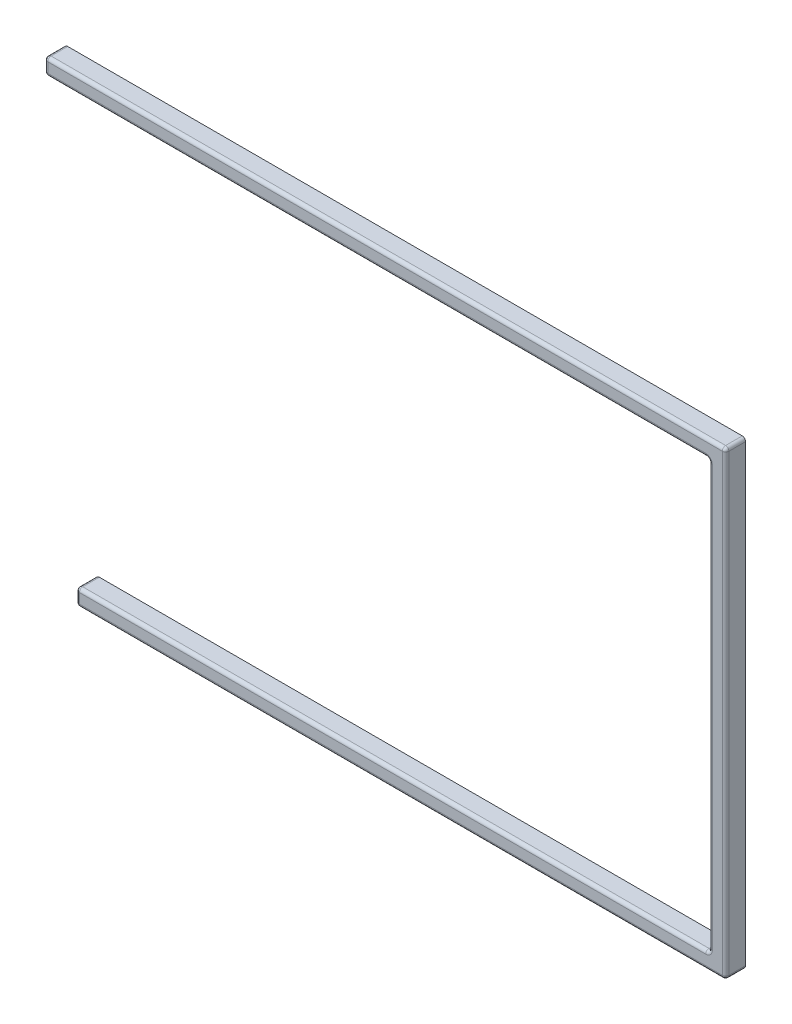
SolidWorks part; units mm, degrees
material "PA 类型 6"
ref_plane "前视基准面" through (0, 0, 0) normal (0, 0, 1) x (1, 0, 0)
ref_plane "上视基准面" through (0, 0, 0) normal (0, 1, 0) x (1, 0, 0)
ref_plane "右视基准面" through (0, 0, 0) normal (1, 0, 0) x (0, 0, -1)
other "Configuration Table"
sketch "Model" plane through (0, 0, 0) normal (0, 0, 1) x (1, 0, 0)
  line L0 (4.8569, 129.021) -> (204.883, 129.021)
  line L1 (204.883, 129.021) -> (204.883, 0.4341)
  line L2 (204.883, 0.4341) -> (14.3819, 0.4341)
  line L3 (21.3817, 112.498) -> (7.3822, 126.497) construction
  line L4 (145.495, 16.9595) -> (159.494, 16.9595)
  line L5 (159.494, 16.9595) -> (159.494, 2.96)
  line L6 (159.494, 2.96) -> (145.495, 2.96)
  line L7 (145.495, 2.96) -> (145.495, 16.9595)
  line L8 (164.545, 16.9595) -> (178.544, 16.9595)
  line L9 (178.544, 16.9595) -> (178.544, 2.96)
  line L10 (178.544, 2.96) -> (164.545, 2.96)
  line L11 (164.545, 2.96) -> (164.545, 16.9595)
  line L12 (183.595, 16.9595) -> (197.594, 16.9595)
  line L13 (197.594, 16.9595) -> (197.594, 2.96)
  line L14 (197.594, 2.96) -> (183.595, 2.96)
  line L15 (183.595, 2.96) -> (183.595, 16.9595)
  line L16 (33.5759, 21.722) -> (33.5759, 17.0215)
  line L17 (33.5759, 17.0215) -> (32.0504, 17.0215)
  line L18 (32.0504, 17.0215) -> (32.0504, 20.2517)
  line L19 (32.0504, 20.2517) -> (30.3251, 20.2517)
  line L20 (30.3251, 20.2517) -> (30.3251, 21.1722)
  line L21 (30.3251, 21.1722) -> (27.0261, 21.1722)
  line L22 (27.0261, 21.1722) -> (27.0261, 20.2517)
  line L23 (27.0261, 20.2517) -> (25.3008, 20.2517)
  line L24 (25.3008, 20.2517) -> (25.3008, 17.0215)
  line L25 (25.3008, 17.0215) -> (24.4753, 17.0215)
  line L26 (24.4753, 17.0215) -> (24.4753, 14.2227)
  line L27 (24.4753, 14.2227) -> (25.3008, 14.2227)
  line L28 (25.3008, 14.2227) -> (25.3008, 7.9527)
  line L29 (25.3008, 7.9527) -> (27.0261, 7.9527)
  line L30 (27.0261, 7.9527) -> (27.0261, 6.9729)
  line L31 (27.0261, 6.9729) -> (30.3251, 6.9729)
  line L32 (30.3251, 6.9729) -> (30.3251, 7.9527)
  line L33 (30.3251, 7.9527) -> (32.0504, 7.9527)
  line L34 (32.0504, 7.9527) -> (32.0504, 12.4216)
  line L35 (32.0504, 12.4216) -> (33.5759, 12.4216)
  line L36 (33.5759, 12.4216) -> (33.5759, 7.7225)
  line L37 (33.5759, 7.7225) -> (47.5753, 7.7225)
  line L38 (47.5753, 7.7225) -> (47.5753, 12.4216)
  line L39 (47.5753, 12.4216) -> (49.101, 12.4216)
  line L40 (49.101, 12.4216) -> (49.101, 7.9527)
  line L41 (49.101, 7.9527) -> (50.8247, 7.9527)
  line L42 (50.8247, 7.9527) -> (50.8247, 6.9729)
  line L43 (50.8247, 6.9729) -> (54.1253, 6.9729)
  line L44 (54.1253, 6.9729) -> (54.1253, 7.9527)
  line L45 (54.1253, 7.9527) -> (55.8504, 7.9527)
  line L46 (55.8504, 7.9527) -> (55.8504, 14.2227)
  line L47 (55.8504, 14.2227) -> (56.6759, 14.2227)
  line L48 (56.6759, 14.2227) -> (56.6759, 17.0215)
  line L49 (56.6759, 17.0215) -> (55.8504, 17.0215)
  line L50 (55.8504, 17.0215) -> (55.8504, 20.2517)
  line L51 (55.8504, 20.2517) -> (54.1253, 20.2517)
  line L52 (54.1253, 20.2517) -> (54.1253, 21.1722)
  line L53 (54.1253, 21.1722) -> (50.8247, 21.1722)
  line L54 (50.8247, 21.1722) -> (50.8247, 20.2517)
  line L55 (50.8247, 20.2517) -> (49.101, 20.2517)
  line L56 (49.101, 20.2517) -> (49.101, 17.0215)
  line L57 (49.101, 17.0215) -> (47.5753, 17.0215)
  line L58 (47.5753, 17.0215) -> (47.5753, 21.722)
  line L59 (47.5753, 21.722) -> (33.5759, 21.722)
  line L60 (71.676, 21.722) -> (85.6753, 21.722)
  line L61 (85.6753, 21.722) -> (85.6753, 7.7225)
  line L62 (85.6753, 7.7225) -> (71.676, 7.7225)
  line L63 (71.676, 7.7225) -> (71.676, 21.722)
  line L64 (95.4871, 21.722) -> (109.488, 21.722)
  line L65 (109.488, 21.722) -> (109.488, 7.7225)
  line L66 (109.488, 7.7225) -> (95.4871, 7.7225)
  line L67 (95.4871, 7.7225) -> (95.4871, 21.722)
  line L68 (119.301, 21.722) -> (133.3, 21.722)
  line L69 (133.3, 21.722) -> (133.3, 7.7225)
  line L70 (133.3, 7.7225) -> (119.301, 7.7225)
  line L71 (119.301, 7.7225) -> (119.301, 21.722)
  line L72 (164.545, 36.0094) -> (178.544, 36.0094)
  line L73 (178.544, 36.0094) -> (178.544, 22.01)
  line L74 (178.544, 22.01) -> (164.545, 22.01)
  line L75 (164.545, 22.01) -> (164.545, 36.0094)
  line L76 (26.4322, 40.7719) -> (40.4315, 40.7719)
  line L77 (40.4315, 40.7719) -> (40.4315, 26.7725)
  line L78 (40.4315, 26.7725) -> (26.4322, 26.7725)
  line L79 (26.4322, 26.7725) -> (26.4322, 40.7719)
  line L80 (45.4822, 40.7719) -> (59.4815, 40.7719)
  line L81 (59.4815, 40.7719) -> (59.4815, 26.7725)
  line L82 (59.4815, 26.7725) -> (45.4822, 26.7725)
  line L83 (45.4822, 26.7725) -> (45.4822, 40.7719)
  line L84 (64.5322, 40.7719) -> (78.5315, 40.7719)
  line L85 (78.5315, 40.7719) -> (78.5315, 26.7725)
  line L86 (78.5315, 26.7725) -> (64.5322, 26.7725)
  line L87 (64.5322, 26.7725) -> (64.5322, 40.7719)
  line L88 (83.5822, 40.7719) -> (97.5815, 40.7719)
  line L89 (97.5815, 40.7719) -> (97.5815, 26.7725)
  line L90 (97.5815, 26.7725) -> (83.5822, 26.7725)
  line L91 (83.5822, 26.7725) -> (83.5822, 40.7719)
  line L92 (102.632, 40.7719) -> (116.632, 40.7719)
  line L93 (116.632, 40.7719) -> (116.632, 26.7725)
  line L94 (116.632, 26.7725) -> (102.632, 26.7725)
  line L95 (102.632, 26.7725) -> (102.632, 40.7719)
  line L96 (128.826, 40.7719) -> (142.825, 40.7719)
  line L97 (142.825, 40.7719) -> (142.825, 26.7725)
  line L98 (142.825, 26.7725) -> (128.826, 26.7725)
  line L99 (128.826, 26.7725) -> (128.826, 40.7719)
  line L100 (188.357, 40.7719) -> (202.357, 40.7719)
  line L101 (202.357, 40.7719) -> (202.357, 26.7725)
  line L102 (202.357, 26.7725) -> (188.357, 26.7725)
  line L103 (188.357, 26.7725) -> (188.357, 40.7719)
  line L104 (143.112, 59.8219) -> (143.112, 55.1215)
  line L105 (143.112, 55.1215) -> (141.588, 55.1215)
  line L106 (141.588, 55.1215) -> (141.588, 58.3516)
  line L107 (141.588, 58.3516) -> (139.863, 58.3516)
  line L108 (139.863, 58.3516) -> (139.863, 59.2723)
  line L109 (139.863, 59.2723) -> (136.562, 59.2723)
  line L110 (136.562, 59.2723) -> (136.562, 58.3516)
  line L111 (136.562, 58.3516) -> (134.837, 58.3516)
  line L112 (134.837, 58.3516) -> (134.837, 55.1215)
  line L113 (134.837, 55.1215) -> (134.013, 55.1215)
  line L114 (134.013, 55.1215) -> (134.013, 52.3226)
  line L115 (134.013, 52.3226) -> (134.837, 52.3226)
  line L116 (134.837, 52.3226) -> (134.837, 46.0527)
  line L117 (134.837, 46.0527) -> (136.562, 46.0527)
  line L118 (136.562, 46.0527) -> (136.562, 45.0716)
  line L119 (136.562, 45.0716) -> (139.863, 45.0716)
  line L120 (139.863, 45.0716) -> (139.863, 46.0527)
  line L121 (139.863, 46.0527) -> (141.588, 46.0527)
  line L122 (141.588, 46.0527) -> (141.588, 50.5217)
  line L123 (141.588, 50.5217) -> (143.112, 50.5217)
  line L124 (143.112, 50.5217) -> (143.112, 45.8227)
  line L125 (143.112, 45.8227) -> (157.113, 45.8227)
  line L126 (157.113, 45.8227) -> (157.113, 50.5217)
  line L127 (157.113, 50.5217) -> (158.637, 50.5217)
  line L128 (158.637, 50.5217) -> (158.637, 46.0527)
  line L129 (158.637, 46.0527) -> (160.362, 46.0527)
  line L130 (160.362, 46.0527) -> (160.362, 45.0716)
  line L131 (160.362, 45.0716) -> (163.663, 45.0716)
  line L132 (163.663, 45.0716) -> (163.663, 46.0527)
  line L133 (163.663, 46.0527) -> (165.388, 46.0527)
  line L134 (165.388, 46.0527) -> (165.388, 52.3226)
  line L135 (165.388, 52.3226) -> (166.212, 52.3226)
  line L136 (166.212, 52.3226) -> (166.212, 55.1215)
  line L137 (166.212, 55.1215) -> (165.388, 55.1215)
  line L138 (165.388, 55.1215) -> (165.388, 58.3516)
  line L139 (165.388, 58.3516) -> (163.663, 58.3516)
  line L140 (163.663, 58.3516) -> (163.663, 59.2723)
  line L141 (163.663, 59.2723) -> (160.362, 59.2723)
  line L142 (160.362, 59.2723) -> (160.362, 58.3516)
  line L143 (160.362, 58.3516) -> (158.637, 58.3516)
  line L144 (158.637, 58.3516) -> (158.637, 55.1215)
  line L145 (158.637, 55.1215) -> (157.113, 55.1215)
  line L146 (157.113, 55.1215) -> (157.113, 59.8219)
  line L147 (157.113, 59.8219) -> (143.112, 59.8219)
  line L148 (16.9072, 59.8219) -> (30.9066, 59.8219)
  line L149 (30.9066, 59.8219) -> (30.9066, 45.8227)
  line L150 (30.9066, 45.8227) -> (16.9072, 45.8227)
  line L151 (16.9072, 45.8227) -> (16.9072, 59.8219)
  line L152 (35.9572, 59.8219) -> (49.9565, 59.8219)
  line L153 (49.9565, 59.8219) -> (49.9565, 45.8227)
  line L154 (49.9565, 45.8227) -> (35.9572, 45.8227)
  line L155 (35.9572, 45.8227) -> (35.9572, 59.8219)
  line L156 (55.0072, 59.8219) -> (69.0065, 59.8219)
  line L157 (69.0065, 59.8219) -> (69.0065, 45.8227)
  line L158 (69.0065, 45.8227) -> (55.0072, 45.8227)
  line L159 (55.0072, 45.8227) -> (55.0072, 59.8219)
  line L160 (74.0572, 59.8219) -> (88.0565, 59.8219)
  line L161 (88.0565, 59.8219) -> (88.0565, 45.8227)
  line L162 (88.0565, 45.8227) -> (74.0572, 45.8227)
  line L163 (74.0572, 45.8227) -> (74.0572, 59.8219)
  line L164 (93.1072, 59.8219) -> (107.107, 59.8219)
  line L165 (107.107, 59.8219) -> (107.107, 45.8227)
  line L166 (107.107, 45.8227) -> (93.1072, 45.8227)
  line L167 (93.1072, 45.8227) -> (93.1072, 59.8219)
  line L168 (112.157, 59.8219) -> (126.157, 59.8219)
  line L169 (126.157, 59.8219) -> (126.157, 45.8227)
  line L170 (126.157, 45.8227) -> (112.157, 45.8227)
  line L171 (112.157, 45.8227) -> (112.157, 59.8219)
  line L172 (188.357, 59.8219) -> (202.357, 59.8219)
  line L173 (202.357, 59.8219) -> (202.357, 45.8227)
  line L174 (202.357, 45.8227) -> (188.357, 45.8227)
  line L175 (188.357, 45.8227) -> (188.357, 59.8219)
  line L176 (12.1447, 78.8719) -> (26.1441, 78.8719)
  line L177 (26.1441, 78.8719) -> (26.1441, 64.8727)
  line L178 (26.1441, 64.8727) -> (12.1447, 64.8727)
  line L179 (12.1447, 64.8727) -> (12.1447, 78.8719)
  line L180 (31.1947, 78.8719) -> (45.194, 78.8719)
  line L181 (45.194, 78.8719) -> (45.194, 64.8727)
  line L182 (45.194, 64.8727) -> (31.1947, 64.8727)
  line L183 (31.1947, 64.8727) -> (31.1947, 78.8719)
  line L184 (50.2447, 78.8719) -> (64.244, 78.8719)
  line L185 (64.244, 78.8719) -> (64.244, 64.8727)
  line L186 (64.244, 64.8727) -> (50.2447, 64.8727)
  line L187 (50.2447, 64.8727) -> (50.2447, 78.8719)
  line L188 (69.2947, 78.8719) -> (83.294, 78.8719)
  line L189 (83.294, 78.8719) -> (83.294, 64.8727)
  line L190 (83.294, 64.8727) -> (69.2947, 64.8727)
  line L191 (69.2947, 64.8727) -> (69.2947, 78.8719)
  line L192 (88.3447, 78.8719) -> (102.344, 78.8719)
  line L193 (102.344, 78.8719) -> (102.344, 64.8727)
  line L194 (102.344, 64.8727) -> (88.3447, 64.8727)
  line L195 (88.3447, 64.8727) -> (88.3447, 78.8719)
  line L196 (107.395, 78.8719) -> (121.394, 78.8719)
  line L197 (121.394, 78.8719) -> (121.394, 64.8727)
  line L198 (121.394, 64.8727) -> (107.395, 64.8727)
  line L199 (107.395, 64.8727) -> (107.395, 78.8719)
  line L200 (126.445, 78.8719) -> (140.444, 78.8719)
  line L201 (140.444, 78.8719) -> (140.444, 64.8727)
  line L202 (140.444, 64.8727) -> (126.445, 64.8727)
  line L203 (126.445, 64.8727) -> (126.445, 78.8719)
  line L204 (150.257, 78.8719) -> (164.257, 78.8719)
  line L205 (164.257, 78.8719) -> (164.257, 64.8727)
  line L206 (164.257, 64.8727) -> (150.257, 64.8727)
  line L207 (150.257, 64.8727) -> (150.257, 78.8719)
  line L208 (188.357, 78.8719) -> (202.357, 78.8719)
  line L209 (202.357, 78.8719) -> (202.357, 64.8727)
  line L210 (202.357, 64.8727) -> (188.357, 64.8727)
  line L211 (188.357, 64.8727) -> (188.357, 78.8719)
  line L212 (145.493, 97.9219) -> (145.493, 93.2215)
  line L213 (145.493, 93.2215) -> (143.969, 93.2215)
  line L214 (143.969, 93.2215) -> (143.969, 96.4516)
  line L215 (143.969, 96.4516) -> (142.244, 96.4516)
  line L216 (142.244, 96.4516) -> (142.244, 97.3723)
  line L217 (142.244, 97.3723) -> (138.943, 97.3723)
  line L218 (138.943, 97.3723) -> (138.943, 96.4516)
  line L219 (138.943, 96.4516) -> (137.218, 96.4516)
  line L220 (137.218, 96.4516) -> (137.218, 93.2215)
  line L221 (137.218, 93.2215) -> (136.394, 93.2215)
  line L222 (136.394, 93.2215) -> (136.394, 90.4226)
  line L223 (136.394, 90.4226) -> (137.218, 90.4226)
  line L224 (137.218, 90.4226) -> (137.218, 84.1527)
  line L225 (137.218, 84.1527) -> (138.943, 84.1527)
  line L226 (138.943, 84.1527) -> (138.943, 83.1716)
  line L227 (138.943, 83.1716) -> (142.244, 83.1716)
  line L228 (142.244, 83.1716) -> (142.244, 84.1527)
  line L229 (142.244, 84.1527) -> (143.969, 84.1527)
  line L230 (143.969, 84.1527) -> (143.969, 88.6217)
  line L231 (143.969, 88.6217) -> (145.493, 88.6217)
  line L232 (145.493, 88.6217) -> (145.493, 83.9227)
  line L233 (145.493, 83.9227) -> (159.494, 83.9227)
  line L234 (159.494, 83.9227) -> (159.494, 88.6217)
  line L235 (159.494, 88.6217) -> (161.018, 88.6217)
  line L236 (161.018, 88.6217) -> (161.018, 84.1527)
  line L237 (161.018, 84.1527) -> (162.743, 84.1527)
  line L238 (162.743, 84.1527) -> (162.743, 83.1716)
  line L239 (162.743, 83.1716) -> (166.044, 83.1716)
  line L240 (166.044, 83.1716) -> (166.044, 84.1527)
  line L241 (166.044, 84.1527) -> (167.768, 84.1527)
  line L242 (167.768, 84.1527) -> (167.768, 90.4226)
  line L243 (167.768, 90.4226) -> (168.593, 90.4226)
  line L244 (168.593, 90.4226) -> (168.593, 93.2215)
  line L245 (168.593, 93.2215) -> (167.768, 93.2215)
  line L246 (167.768, 93.2215) -> (167.768, 96.4516)
  line L247 (167.768, 96.4516) -> (166.044, 96.4516)
  line L248 (166.044, 96.4516) -> (166.044, 97.3723)
  line L249 (166.044, 97.3723) -> (162.743, 97.3723)
  line L250 (162.743, 97.3723) -> (162.743, 96.4516)
  line L251 (162.743, 96.4516) -> (161.018, 96.4516)
  line L252 (161.018, 96.4516) -> (161.018, 93.2215)
  line L253 (161.018, 93.2215) -> (159.494, 93.2215)
  line L254 (159.494, 93.2215) -> (159.494, 97.9219)
  line L255 (159.494, 97.9219) -> (145.493, 97.9219)
  line L256 (2.6197, 97.9219) -> (16.6192, 97.9219)
  line L257 (16.6192, 97.9219) -> (16.6192, 83.9227)
  line L258 (16.6192, 83.9227) -> (2.6197, 83.9227)
  line L259 (2.6197, 83.9227) -> (2.6197, 97.9219)
  line L260 (21.6697, 97.9219) -> (35.669, 97.9219)
  line L261 (35.669, 97.9219) -> (35.669, 83.9227)
  line L262 (35.669, 83.9227) -> (21.6697, 83.9227)
  line L263 (21.6697, 83.9227) -> (21.6697, 97.9219)
  line L264 (40.7197, 97.9219) -> (54.719, 97.9219)
  line L265 (54.719, 97.9219) -> (54.719, 83.9227)
  line L266 (54.719, 83.9227) -> (40.7197, 83.9227)
  line L267 (40.7197, 83.9227) -> (40.7197, 97.9219)
  line L268 (59.7697, 97.9219) -> (73.769, 97.9219)
  line L269 (73.769, 97.9219) -> (73.769, 83.9227)
  line L270 (73.769, 83.9227) -> (59.7697, 83.9227)
  line L271 (59.7697, 83.9227) -> (59.7697, 97.9219)
  line L272 (78.8197, 97.9219) -> (92.819, 97.9219)
  line L273 (92.819, 97.9219) -> (92.819, 83.9227)
  line L274 (92.819, 83.9227) -> (78.8197, 83.9227)
  line L275 (78.8197, 83.9227) -> (78.8197, 97.9219)
  line L276 (97.8683, 97.9219) -> (111.869, 97.9219)
  line L277 (111.869, 97.9219) -> (111.869, 83.9227)
  line L278 (111.869, 83.9227) -> (97.8683, 83.9227)
  line L279 (97.8683, 83.9227) -> (97.8683, 97.9219)
  line L280 (116.918, 97.9219) -> (130.919, 97.9219)
  line L281 (130.919, 97.9219) -> (130.919, 83.9227)
  line L282 (130.919, 83.9227) -> (116.918, 83.9227)
  line L283 (116.918, 83.9227) -> (116.918, 97.9219)
  line L284 (188.357, 97.9219) -> (202.357, 97.9219)
  line L285 (202.357, 97.9219) -> (202.357, 83.9227)
  line L286 (202.357, 83.9227) -> (188.357, 83.9227)
  line L287 (188.357, 83.9227) -> (188.357, 97.9219)
  line L288 (7.3822, 126.497) -> (21.3817, 126.497)
  line L289 (21.3817, 126.497) -> (21.3817, 112.498)
  line L290 (21.3817, 112.498) -> (7.3822, 112.498)
  line L291 (7.3822, 112.498) -> (7.3822, 126.497)
  line L292 (26.4322, 126.497) -> (40.4315, 126.497)
  line L293 (40.4315, 126.497) -> (40.4315, 112.498)
  line L294 (40.4315, 112.498) -> (26.4322, 112.498)
  line L295 (26.4322, 112.498) -> (26.4322, 126.497)
  line L296 (45.4822, 126.497) -> (59.4815, 126.497)
  line L297 (59.4815, 126.497) -> (59.4815, 112.498)
  line L298 (59.4815, 112.498) -> (45.4822, 112.498)
  line L299 (45.4822, 112.498) -> (45.4822, 126.497)
  line L300 (64.5322, 126.497) -> (78.5315, 126.497)
  line L301 (78.5315, 126.497) -> (78.5315, 112.498)
  line L302 (78.5315, 112.498) -> (64.5322, 112.498)
  line L303 (64.5322, 112.498) -> (64.5322, 126.497)
  line L304 (83.5822, 126.497) -> (97.5815, 126.497)
  line L305 (97.5815, 126.497) -> (97.5815, 112.498)
  line L306 (97.5815, 112.498) -> (83.5822, 112.498)
  line L307 (83.5822, 112.498) -> (83.5822, 126.497)
  line L308 (102.632, 126.497) -> (116.632, 126.497)
  line L309 (116.632, 126.497) -> (116.632, 112.498)
  line L310 (116.632, 112.498) -> (102.632, 112.498)
  line L311 (102.632, 112.498) -> (102.632, 126.497)
  line L312 (121.682, 126.497) -> (135.682, 126.497)
  line L313 (135.682, 126.497) -> (135.682, 112.498)
  line L314 (135.682, 112.498) -> (121.682, 112.498)
  line L315 (121.682, 112.498) -> (121.682, 126.497)
  line L316 (145.495, 126.497) -> (159.494, 126.497)
  line L317 (159.494, 126.497) -> (159.494, 112.498)
  line L318 (159.494, 112.498) -> (145.495, 112.498)
  line L319 (145.495, 112.498) -> (145.495, 126.497)
  line L320 (164.545, 126.497) -> (178.544, 126.497)
  line L321 (178.544, 126.497) -> (178.544, 112.498)
  line L322 (178.544, 112.498) -> (164.545, 112.498)
  line L323 (164.545, 112.498) -> (164.545, 126.497)
  line L324 (185.976, 126.497) -> (199.975, 126.497)
  line L325 (199.975, 126.497) -> (199.975, 112.498)
  line L326 (199.975, 112.498) -> (185.976, 112.498)
  line L327 (185.976, 112.498) -> (185.976, 126.497)
  line L328 (0.0939, 81.391) -> (0.0939, 109.971)
  line L329 (14.3819, 24.241) -> (14.3819, 0.4341)
  line L435 (0.0939, 109.971) -> (4.8569, 109.971)
  line L436 (4.8569, 109.971) -> (4.8569, 129.021)
  line L437 (0.0939, 81.391) -> (9.6189, 81.391)
  line L438 (9.6189, 81.391) -> (9.6189, 62.341)
  line L439 (9.6189, 62.341) -> (14.3819, 62.341)
  line L440 (14.3819, 62.341) -> (14.3819, 43.291)
  line L441 (14.3819, 43.291) -> (23.9069, 43.291)
  line L442 (23.9069, 43.291) -> (23.9069, 24.241)
  line L443 (23.9069, 24.241) -> (14.3819, 24.241)
  point P328 (14.3819, 119.4975)
  dimension "D1" = 19.05
  dimension "D2" = 4.763
  dimension "D3" = 28.58
  dimension "D4" = 9.525
  dimension "D5" = 9.525
extrude "凸台-拉伸1" add sketch "Model" along normal blind 3
sketch "草图1" plane through (0, 0, 3) normal (0, 0, 1) x (1, 0, 0)
  line L3 (14.3819, 0.4341) -> (204.883, 0.4341) construction
  line L4 (204.883, 0.4341) -> (204.883, 129.021) construction
  line L5 (204.883, 129.021) -> (4.8569, 129.021) construction
  line L6 (14.3819, -4.5659) -> (209.883, -4.5659)
  line L7 (209.883, -4.5659) -> (209.883, 134.021)
  line L8 (209.883, 134.021) -> (4.8569, 134.021)
  line L9 (14.3819, -4.5659) -> (209.883, -4.5659)
  line L10 (209.883, -4.5659) -> (209.883, 134.021)
  line L11 (209.883, 134.021) -> (4.8569, 134.021)
  line L12 (14.3819, 0.4341) -> (204.883, 0.4341)
  line L13 (204.883, 0.4341) -> (204.883, 129.021)
  line L14 (204.883, 129.021) -> (4.8569, 129.021)
  line L15 (4.8569, 129.021) -> (4.8569, 134.021)
  line L16 (14.3819, -4.5659) -> (14.3819, 0.4341)
  dimension "D1" = 5
extrude "凸台-拉伸2" add sketch "草图1" along normal blind 6 from surface at -3 starting at face at (38.8748, 64.3843, 0)
sketch "草图2" plane through (0, 0, 3) normal (0, 0, 1) x (1, 0, 0)
  line L0 (14.3819, -4.5659) -> (209.883, -4.5659) construction
  line L1 (14.3819, 24.241) -> (14.3819, 0.4341) construction
  line L2 (209.883, 134.021) -> (4.8569, 134.021) construction
  line L3 (4.8569, 129.021) -> (4.8569, 109.971) construction
  circle A0 centre (7.8569, 131.521) radius 1.25
  circle A1 centre (17.3819, -2.0659) radius 1.25
  dimension "D1" = 2.5
  dimension "D4" = 2.5
  dimension "D2" = 2.5
  dimension "D3" = 3
  dimension "D5" = 2.5
  dimension "D6" = 3
extrude "切除-拉伸1" cut sketch "草图2" along normal blind 3.5 from surface at -3 starting at face at (39.5891, 64.3843, 0)
fillet "圆角1" radius 1 4 edges at (14.3819, -4.5659, 3) (4.8569, 134.021, 3) (209.883, 134.021, 3) (209.883, -4.5659, 3)
pattern_linear "阵列(线性)1" count 3 spacing 90 along (1, 0, 0) of "切除-拉伸1"
sketch "草图3" plane through (0, 0, 3) normal (0, 0, 1) x (1, 0, 0)
  line L0 (209.883, -3.5659) -> (209.883, 133.021) construction
  line L1 (15.3819, -4.5659) -> (208.883, -4.5659) construction
  circle A0 centre (207.383, 35.4341) radius 1.25
  dimension "D1" = 2.5
  dimension "D2" = 2.5
  dimension "D3" = 40
extrude "切除-拉伸2" cut sketch "草图3" along normal blind 3.5 from surface at -3 starting at face at (106.1319, -2.0659, 0)
pattern_linear "阵列(线性)2" count 3 spacing 70 along (0, 1, 0) of "切除-拉伸2"
sketch "草图4" plane through (0, 0, 3) normal (0, 0, 1) x (1, 0, 0)
  line L0 (14.3819, 0.4341) -> (204.883, 0.4341) construction
  line L1 (204.883, 0.4341) -> (204.883, 129.021) construction
  line L2 (204.883, 129.021) -> (4.8569, 129.021) construction
  line L3 (14.3819, 0.4341) -> (204.883, 0.4341)
  line L4 (204.883, 0.4341) -> (204.883, 129.021)
  line L5 (204.883, 129.021) -> (4.8569, 129.021)
  line L6 (4.8569, 129.021) -> (0.0939, 129.021)
  line L7 (0.0939, 129.021) -> (0.0939, 0.4341)
  line L8 (0.0939, 0.4341) -> (14.3819, 0.4341)
  line L9 (0.0939, 109.971) -> (0.0939, 81.391) construction
extrude "切除-拉伸3" cut sketch "草图4" against normal blind 10
fillet "圆角2" radius 1 16 edges at (109.6325, 0.4341, 6) (204.883, 64.7275, 6) (104.87, 129.021, 6) (4.8569, 131.021, 6) (5.1498, 133.7281, 6) (107.37, 134.021, 6) (209.5901, 133.7281, 6) (209.883, 64.7275, 6) (209.5901, -4.273, 6) (112.1325, -4.5659, 6) (14.6748, -4.273, 6) (14.3819, -1.5659, 6) (204.883, 0.4341, 3) (204.883, 129.021, 3) (14.3819, 0.4341, 3) (4.8569, 129.021, 3)
